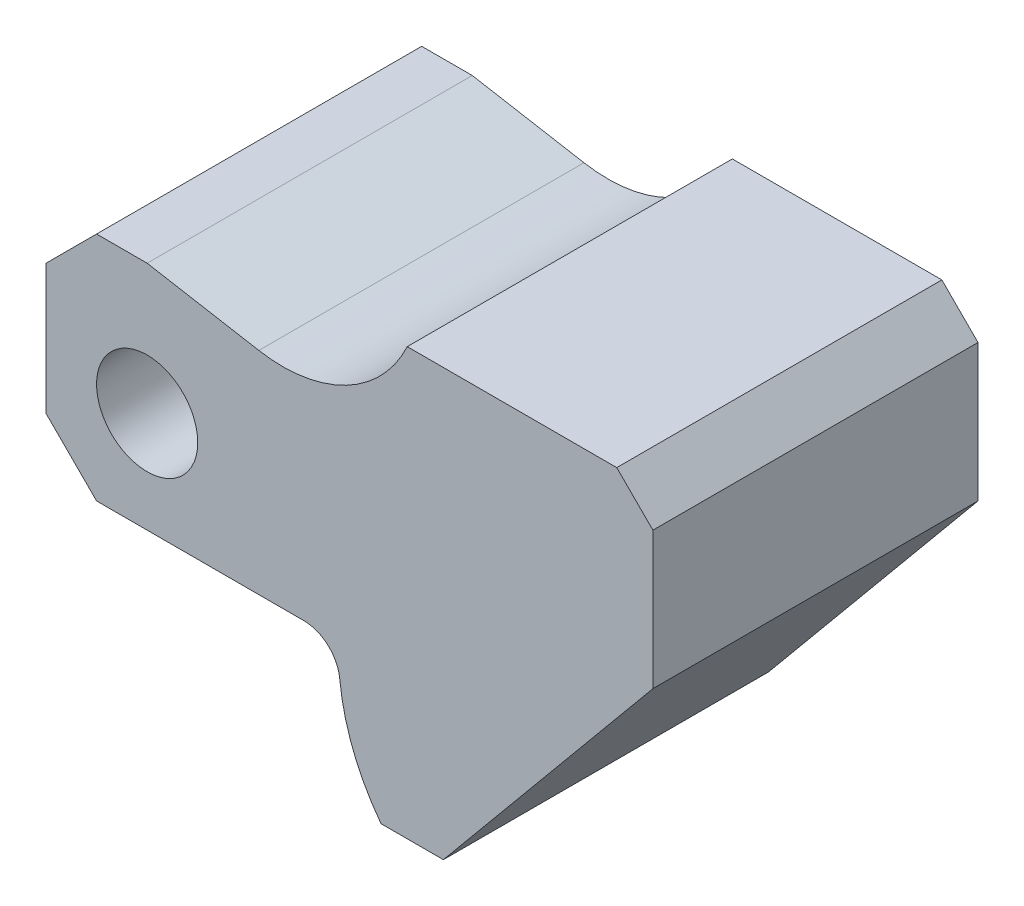
SolidWorks part; units mm, degrees
material "AISI 1020"
ref_plane "Front Plane" through (0, 0, 0) normal (0, 0, 1) x (1, 0, 0)
ref_plane "Top Plane" through (0, 0, 0) normal (0, 1, 0) x (1, 0, 0)
ref_plane "Right Plane" through (0, 0, 0) normal (1, 0, 0) x (0, 0, -1)
sketch "Sketch2" plane through (0, 0, 0) normal (0, 0, 1) x (1, 0, 0)
  line L0 (-14, 11) -> (-14, -7)
  line L1 (-14, -7) -> (-7, -14)
  line L2 (-7, -14) -> (21.6806, -14)
  line L3 (-14, 11) -> (-7, 18)
  line L4 (-7, 18) -> (0, 18)
  line L5 (0, 18) -> (15.4602, 15.274)
  line L6 (36, 26) -> (65, 26)
  line L7 (65, 26) -> (70, 21)
  line L8 (70, 21) -> (70, 2)
  line L9 (70, 2) -> (41, -33)
  line L10 (41, -33) -> (32.3753, -33)
  circle A0 centre (0, 0) radius 7
  arc A1 (15.4602, 15.274) -> (36, 26) centre (18.7595, 33.9853) ccw
  arc A2 (26.6541, -18.4853) -> (32.3753, -33) centre (55.5, -15.5) ccw
  arc A3 (21.6806, -14) -> (26.6541, -18.4853) centre (21.6806, -19) cw
  dimension "D1" = 14
  dimension "D9" = 19
  dimension "D11" = 5
  dimension "D15" = 29
  dimension "D2" = 7
  dimension "D3" = 7
  dimension "D4" = 45
  dimension "D5" = 45
  dimension "D6" = 14
  dimension "D7" = 14
  dimension "D8" = 32
  dimension "D10" = 10
  dimension "D12" = 14
  dimension "D13" = 45
  dimension "D14" = 5
  dimension "D16" = 29
  dimension "D17" = 59
  dimension "D18" = 24
  dimension "D19" = 19
  dimension "D20" = 84
  dimension "D21" = 29
extrude "Boss-Extrude1" add sketch "Sketch2" along normal blind 45
